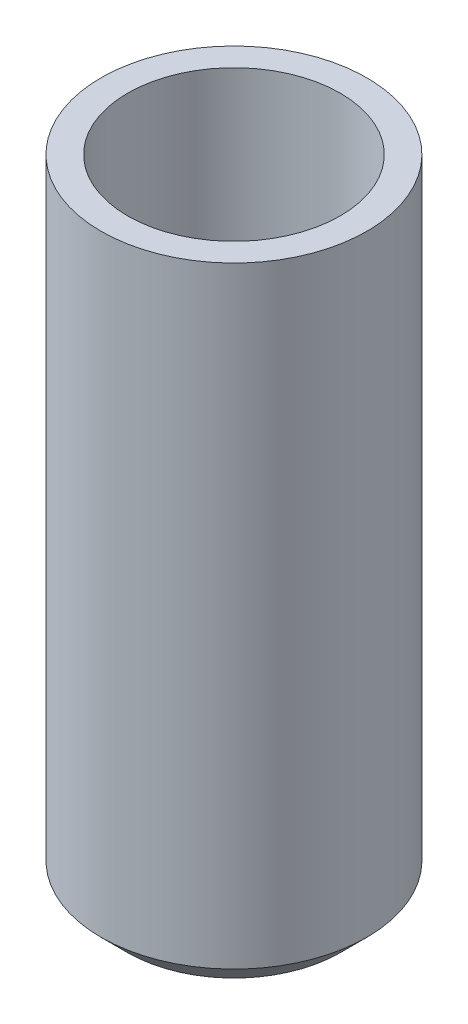
SolidWorks part; units mm, degrees
ref_plane "Front Plane" through (0, 0, 0) normal (0, 0, 1) x (1, 0, 0)
ref_plane "Top Plane" through (0, 0, 0) normal (0, 1, 0) x (1, 0, 0)
ref_plane "Right Plane" through (0, 0, 0) normal (1, 0, 0) x (0, 0, -1)
sketch "Sketch1" plane through (0, 0, 0) normal (0, 0, 1) x (1, 0, 0)
  line L0 (0, 120.7745) -> (0, -52.3842) construction
  line L1 (0, 0) -> (2, 0)
  line L2 (2.5, 0.5) -> (2.5, 12)
  line L3 (2.5, 12) -> (0, 12)
  line L4 (0, 12) -> (0, 0)
  line L5 (2, 0) -> (2.5, 0.5)
  point P4 (2.5, 0)
  dimension "D1" = 5
  dimension "D2" = 12
  dimension "D3" = 0.5
  dimension "D4" = 45
revolve "Revolve1" add sketch "Sketch1" angle 360 about L0
sketch "Sketch2" plane through (0, 12, 0) normal (0, 1, 0) x (1, 0, 0)
  circle A0 centre (0, 0) radius 2
  dimension "D1" = 4
extrude "Cut-Extrude1" cut sketch "Sketch2" against normal blind 8
